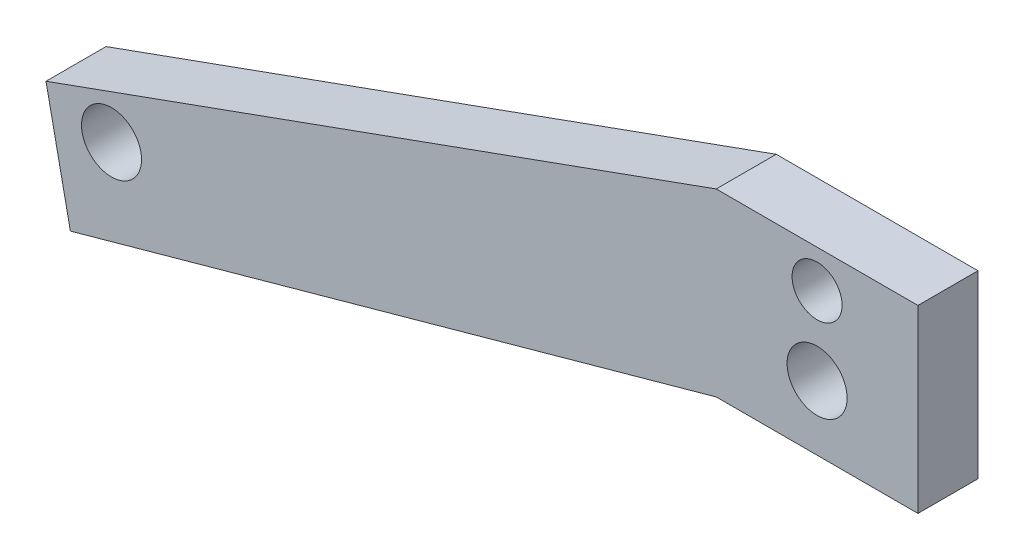
SolidWorks part; units mm, degrees
ref_plane "Front Plane" through (0, 0, 0) normal (0, 0, 1) x (1, 0, 0)
ref_plane "Top Plane" through (0, 0, 0) normal (0, 1, 0) x (1, 0, 0)
ref_plane "Right Plane" through (0, 0, 0) normal (1, 0, 0) x (0, 0, -1)
sketch "Sketch1" plane through (0, 0, 0) normal (0, 0, 1) x (1, 0, 0)
  line L0 (-16, 45) -> (-122.3101, 6.6416)
  line L2 (-276.7879, -13.7825) -> (-251.7788, -35.3347) construction
  line L3 (0, 26.6476) -> (-111.9216, 3.4517) construction
  line L4 (-16, 45) -> (-16, 15)
  line L5 (-16, 15) -> (16, 15)
  line L6 (16, 15) -> (16, 45)
  line L7 (16, 45) -> (-16, 45)
  line L8 (-16, 45) -> (-16, 16.425) construction
  line L9 (-16, 15) -> (16, 15) construction
  line L10 (16, 16.425) -> (16, 45)
  line L11 (16, 45) -> (-16, 45)
  line L12 (16, 16.425) -> (-16, 16.425)
  line L13 (-16, 16.425) -> (-118.4441, -12.012)
  line L14 (-118.4441, -12.012) -> (-122.3101, 6.6416)
  line L15 (-251.7788, -35.3347) -> (-242.2031, -37.4927) construction
  line L17 (-31.1634, 26.3038) -> (-28.9161, 26.7) construction
  line L18 (-2118.0351, -341.6) -> (-28.9161, 26.7) construction
  line L19 (-242.2031, -37.4927) -> (-208.8903, -37.4927) construction
  line L20 (-208.8903, -37.4927) -> (-16, 45) construction
  line L21 (-292.5067, -43.5335) -> (-248.9466, -55.1606) construction
  line L22 (-248.9466, -55.1606) -> (-208.8903, -56.2396) construction
  line L23 (-208.8903, -56.2396) -> (-14.9476, 16.425) construction
  line L24 (-288.0555, -26.8574) -> (0, 26.6476) construction
  circle A0 centre (0, 39) radius 3.9687 construction
  circle A1 centre (0, 39) radius 3.9687
  circle A2 centre (0, 26.6476) radius 4.7625
  circle A3 centre (-111.9216, 3.4517) radius 4.7625
  circle A4 centre (-288.0555, -26.8574) radius 17.26 construction
  dimension "D2" = 9.525
  dimension "D4" = 114.3
  dimension "D7" = 292.9825
  dimension "D3" = 9.525
  dimension "D5" = 19.05
  dimension "D6" = 28.575
  dimension "D8" = 11.709
  dimension "D9" = 160.16
  dimension "D10" = 164.486
  dimension "D1" = 0
extrude "Boss-Extrude1" add sketch "Sketch1" along normal blind 9.525
